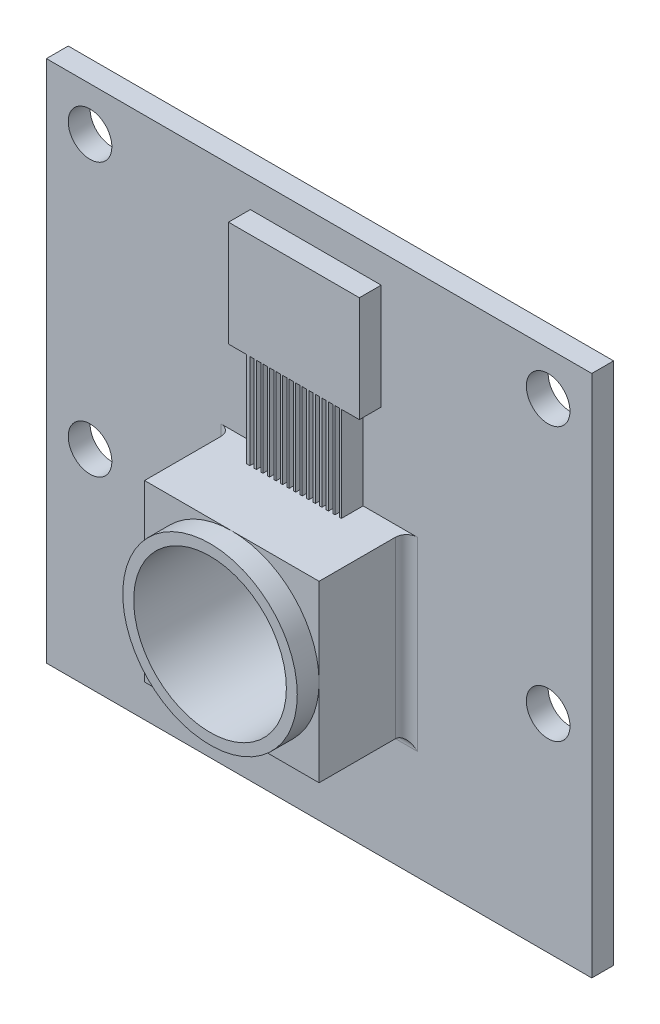
SolidWorks part; units mm, degrees
ref_plane "Front Plane" through (0, 0, 0) normal (0, 0, 1) x (1, 0, 0)
ref_plane "Top Plane" through (0, 0, 0) normal (0, 1, 0) x (1, 0, 0)
ref_plane "Right Plane" through (0, 0, 0) normal (1, 0, 0) x (0, 0, -1)
sketch "Sketch1" plane through (0, 0, 0) normal (0, 0, 1) x (1, 0, 0)
  line L1 (-12.5, 12) -> (12.5, 12)
  line L2 (-12.5, 12) -> (-12.5, -12)
  line L3 (-12.5, -12) -> (12.5, -12)
  line L4 (12.5, 12) -> (12.5, -12)
  line L5 (-12.5, 12) -> (12.5, -12) construction
  line L6 (-12.5, -12) -> (12.5, 12) construction
  circle A0 centre (10.5, 10) radius 1
  circle A1 centre (-10.5, 10) radius 1
  circle A2 centre (-10.5, -2.5) radius 1
  circle A3 centre (10.5, -2.5) radius 1
  point P0 (0, 0)
  dimension "D3" = 2
  dimension "D1" = 24
  dimension "D2" = 25
  dimension "D4" = 2
  dimension "D5" = 2
  dimension "D6" = 2
  dimension "D7" = 2
extrude "Boss-Extrude1" add sketch "Sketch1" along normal blind 1
sketch "Sketch2" plane through (0, 0, 1) normal (0, 0, 1) x (1, 0, 0)
  line L1 (-4, 1.5) -> (4, 1.5)
  line L2 (-4, 1.5) -> (-4, -6.5)
  line L3 (-4, -6.5) -> (4, -6.5)
  line L4 (4, 1.5) -> (4, -6.5)
  line L5 (-4, 1.5) -> (4, -6.5) construction
  line L6 (-4, -6.5) -> (4, 1.5) construction
  point P0 (0, -2.5)
extrude "Boss-Extrude2" add sketch "Sketch2" along normal blind 4
sketch "Sketch3" plane through (0, 0, 5) normal (0, 0, 1) x (1, 0, 0)
  circle A0 centre (0, -2.5) radius 4
extrude "Boss-Extrude3" add sketch "Sketch3" along normal blind 1
fillet "Fillet2" radius 0.5 3 edges at (4, -2.5, 1) (0, -6.5, 1) (-4, -2.5, 1)
sketch "Sketch4" plane through (0, 0, 0) normal (0, 0, -1) x (-1, 0, 0)
  line L0 (12.5, -12) -> (-12.5, -12) construction
  line L1 (-8, -5) -> (8, -5)
  line L2 (-8, -5) -> (-8, -10)
  line L3 (-8, -10) -> (8, -10)
  line L4 (8, -5) -> (8, -10)
  line L5 (-8, -5) -> (8, -10) construction
  line L6 (-8, -10) -> (8, -5) construction
  point P0 (0, 0)
  dimension "D1" = 16
  dimension "D2" = 5
  dimension "D3" = 7
extrude "Boss-Extrude4" add sketch "Sketch4" along normal blind 2
fillet "Fillet3" radius 0.5 12 edges at (0, -5, -2) (0, -5, 0) (0, -10, -2) (0, -10, 0) (8, -5, -1) (8, -7.5, -2) (8, -10, -1) (8, -7.5, 0) (-8, -10, -1) (-8, -7.5, -2) (-8, -5, -1) (-8, -7.5, 0)
sketch "Sketch5" plane through (0, 0, 6) normal (0, 0, 1) x (1, 0, 0)
  circle A0 centre (0, -2.5) radius 3.5
  dimension "D1" = 7
extrude "Cut-Extrude1" cut sketch "Sketch5" against normal blind 6
sketch "Sketch6" plane through (0, 0, 1) normal (0, 0, 1) x (1, 0, 0)
  line L0 (4.5, 1.5) -> (-4.5, 1.5) construction
  line L1 (-3.1525, 5.84) -> (-2.3226, 5.84)
  line L2 (-2.3226, 5.84) -> (-2.3226, 1.5)
  line L3 (-2.3226, 1.5) -> (2.0174, 1.5)
  line L4 (2.0174, 5.84) -> (2.0174, 1.5)
  line L5 (-2.3226, 5.84) -> (2.0174, 1.5) construction
  line L6 (-2.3226, 1.5) -> (2.0174, 5.84) construction
  line L7 (2.6463, 6.4689) -> (2.8469, 6.4689)
  line L8 (-3.1525, 10.68) -> (2.8464, 10.68)
  line L9 (-3.1525, 10.68) -> (-3.1525, 5.84)
  line L10 (-3.152, 6.4689) -> (-2.9515, 6.4689)
  line L11 (2.8464, 10.68) -> (2.8464, 5.84)
  line L12 (-3.1525, 10.68) -> (2.8464, 5.84) construction
  line L13 (-3.1525, 5.84) -> (2.8464, 10.68) construction
  line L14 (2.0174, 5.84) -> (2.8464, 5.84)
  point P0 (-0.1526, 3.67)
  point P7 (-0.1531, 8.26)
  dimension "D1" = 4.34
  dimension "D2" = 4.34
  dimension "D3" = 4.84
extrude "Boss-Extrude5" add sketch "Sketch6" along normal blind 1
sketch "Sketch7" plane through (0, 0, 2) normal (0, 0, 1) x (1, 0, 0)
  line L0 (-2.3226, 1.5) -> (2.0174, 1.5) construction
  line L1 (-2.1726, 1.5) -> (-1.9726, 1.5)
  line L2 (-2.1726, 1.5) -> (-2.1726, 5.84)
  line L3 (-2.1726, 5.84) -> (-1.9726, 5.84)
  line L4 (-1.9726, 1.5) -> (-1.9726, 5.84)
  line L6 (-2.3226, 5.84) -> (-2.3226, 1.5) construction
  dimension "D1" = 0.2
  dimension "D2" = 0.15
extrude "Cut-Extrude2" cut sketch "Sketch7" against normal blind 1
pattern_linear "LPattern1" count 14 spacing 0.3 along (1, 0, 0) of "Cut-Extrude2"
